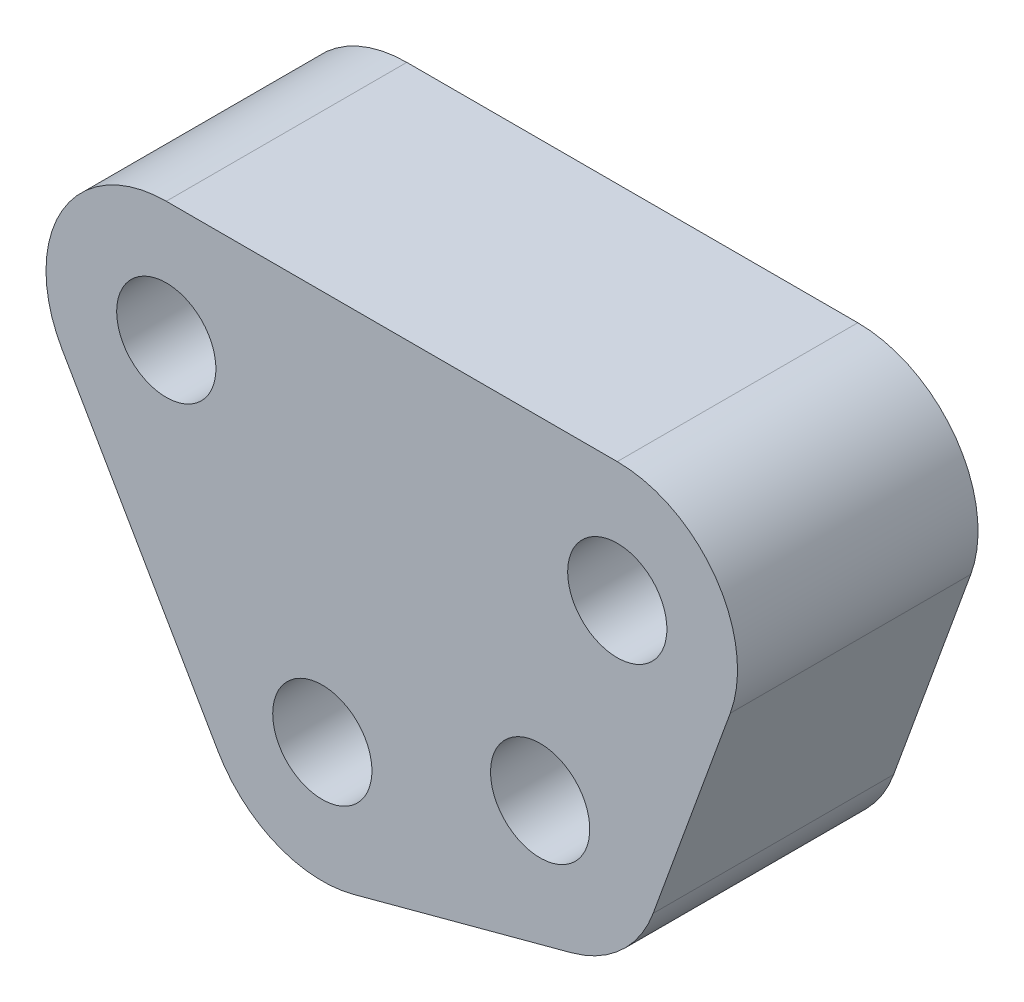
SolidWorks part; units mm, degrees
ref_plane "Plan de face" through (0, 0, 0) normal (0, 0, 1) x (1, 0, 0)
ref_plane "Plan de dessus" through (0, 0, 0) normal (0, 1, 0) x (1, 0, 0)
ref_plane "Plan de droite" through (0, 0, 0) normal (1, 0, 0) x (0, 0, -1)
sketch "Esquisse1" plane through (0, 0, 0) normal (0, 0, 1) x (1, 0, 0)
  line L0 (-15, 4) -> (0, 4)
  line L1 (3.7588, -1.3681) -> (1.1936, -8.4158)
  line L3 (-18.4641, -2) -> (-13.2743, -10.989)
  line L4 (-8.7749, -12.8527) -> (-1.5299, -10.9114)
  line L5 (-15, 0) -> (8.8398, -12.4102) construction
  arc A0 (1.1936, -8.4158) -> (-1.5299, -10.9114) centre (-2.5652, -7.0477) cw
  arc A1 (0, 4) -> (3.7588, -1.3681) centre (0, 0) cw
  arc A2 (-15, 4) -> (-18.4641, -2) centre (-15, 0) ccw
  arc A3 (-13.2743, -10.989) -> (-8.7749, -12.8527) centre (-9.8102, -8.989) ccw
  dimension "D1" = 4
  dimension "D4" = 4
  dimension "D2" = 15
  dimension "D3" = 7.5
  dimension "D5" = 60
  dimension "D6" = 55
  dimension "D7" = 27.5
  dimension "D8" = 70
extrude "Boss.-Extru.1" add sketch "Esquisse1" along normal blind 8
hole_wizard "Trou taraudé M41" positions "Esquisse2" profile "Esquisse3" tap size "M4" standard "ISO" end condition through all
sketch "Esquisse2" plane through (0, 0, 0) normal (0, 0, 1) x (1, 0, 0)
  point P0 (-15, 0)
  point P3 (0, 0)
  point P6 (-2.5652, -7.0477)
  point P9 (-9.8102, -8.989)
sketch "Esquisse3" plane through (-15, 0, 0) normal (1, 0, 0) x (0, 1, 0)
  line L0 (0, 0) -> (0, 8)
  line L1 (0, 8) -> (1.65, 8)
  line L2 (1.65, 8) -> (1.65, 0)
  line L5 (1.65, 0) -> (0, 0)
  line L11 (0, -6.35) -> (0, 107.95) construction
  dimension "Diamètre du trou pour taraudage jusqu'au prochain" = 3.3
  dimension "Profondeur du trou pour taraudage jusqu'au prochain" = 8
cosmetic thread "Filetage de perçage1"
cosmetic thread "Filetage de perçage2"
cosmetic thread "Filetage de perçage3"
cosmetic thread "Filetage de perçage4"
